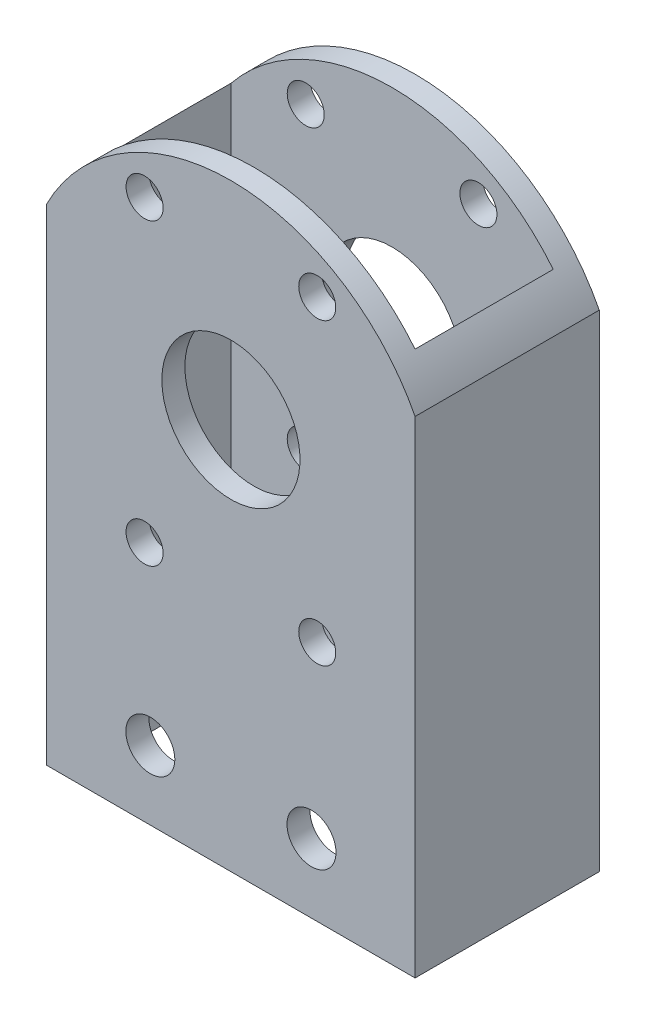
SolidWorks part; units mm, degrees
material "6061-T6 (SS)"
ref_plane "Front" through (0, 0, 0) normal (0, 0, 1) x (1, 0, 0)
ref_plane "Top" through (0, 0, 0) normal (0, 1, 0) x (1, 0, 0)
ref_plane "Right" through (0, 0, 0) normal (1, 0, 0) x (0, 0, -1)
sketch "Sketch1" plane through (0, 0, 0) normal (0, 1, 0) x (1, 0, 0)
  line L1 (-25.4, -12.7) -> (25.4, -12.7)
  line L2 (-25.4, -12.7) -> (-25.4, 12.7)
  line L3 (-25.4, 12.7) -> (25.4, 12.7)
  line L4 (25.4, -12.7) -> (25.4, 12.7)
  line L5 (-25.4, -12.7) -> (25.4, 12.7) construction
  line L6 (-25.4, 12.7) -> (25.4, -12.7) construction
  point P0 (0, 0)
  dimension "D1" = 25.4
  dimension "D2" = 50.8
extrude "Extrude-Thin1" add sketch "Sketch1" along normal blind 82.55 thin thin type one direction reverse wall 3.175
sketch "Sketch2" plane through (0, 0, -12.7) normal (0, 0, -1) x (-1, 0, 0)
  line L0 (0, 82.55) -> (0, 50.8)
  line L1 (-25.4, 82.55) -> (25.4, 82.55) construction
  line L3 (0, 41.275) -> (0, 60.325) construction
  circle A1 centre (0, 50.8) radius 23.8125
  circle A3 centre (0, 50.8) radius 9.525
  point P12 (0, 50.8)
  dimension "D1" = 19.05
  dimension "D3" = 47.625
  dimension "D2" = 31.75
hole_wizard "#10 Clearance Hole1" positions "Sketch5" profile "Sketch6" hole size "#10" standard "ANSI Inch" end condition through all
sketch "Sketch5" plane through (0, 0, -12.7) normal (0, 0, -1) x (-1, 0, 0)
  line L0 (0, 82.55) -> (0, 53.975)
  line L1 (-25.4, 82.55) -> (25.4, 82.55) construction
  line L3 (-11.9063, 74.5972) -> (11.9063, 74.5972)
  line L4 (-11.9063, 74.5972) -> (-11.9063, 33.3528)
  line L5 (-11.9063, 33.3528) -> (11.9063, 33.3528)
  line L6 (11.9063, 74.5972) -> (11.9063, 33.3528)
  circle A0 centre (0, 53.975) radius 23.8125
  point P21 (-11.9063, 74.5972)
  point P22 (11.9063, 74.5972)
  point P24 (11.9063, 33.3528)
  point P25 (-11.9063, 33.3528)
  dimension "D1" = 47.625
  dimension "D2" = 28.575
  dimension "D3" = 23.8125
sketch "Sketch6" plane through (11.9063, 33.3528, -12.7) normal (1, 0, 0) x (0, 1, 0)
  line L0 (0, 0) -> (0, 25.4)
  line L1 (0, 25.4) -> (2.5527, 25.4)
  line L2 (2.5527, 25.4) -> (2.5527, 0)
  line L5 (2.5527, 0) -> (0, 0)
  line L11 (0, -6.35) -> (0, 107.95) construction
  dimension "Thru Hole Dia." = 5.1054
  dimension "Thru Hole Depth" = 25.4
sketch "Sketch7" plane through (0, 0, -12.7) normal (0, 0, -1) x (-1, 0, 0)
  line L0 (-11.9063, 74.5972) -> (11.9063, 33.3528) construction
  circle A1 centre (0, 53.975) radius 9.525
  point P9 (0, 53.975)
  dimension "D1" = 19.05
extrude "Cut-Extrude2" cut sketch "Sketch7" against normal through all both
hole_wizard "1/4 Clearance Hole2" positions "Sketch8" profile "Sketch9" hole size "1/4" standard "ANSI Inch" end condition through all
sketch "Sketch8" plane through (0, 0, 12.7) normal (0, 0, 1) x (1, 0, 0)
  line L2 (-25.4, 82.55) -> (-25.4, 0) construction
  line L4 (-25.4, 0) -> (25.4, 0) construction
  point P0 (-11.1125, 9.525)
  point P2 (11.1125, 9.525)
  point P14 (-109.1715, 68.7854)
  dimension "D1" = 22.225
  dimension "D2" = 14.2875
  dimension "D3" = 9.525
sketch "Sketch9" plane through (-11.1125, 9.525, 12.7) normal (1, 0, 0) x (0, -1, 0)
  line L0 (0, 0) -> (0, 25.4)
  line L1 (0, 25.4) -> (3.3782, 25.4)
  line L2 (3.3782, 25.4) -> (3.3782, 0)
  line L5 (3.3782, 0) -> (0, 0)
  line L11 (0, -6.35) -> (0, 107.95) construction
  dimension "Thru Hole Dia." = 6.7564
  dimension "Thru Hole Depth" = 25.4
sketch "Sketch10" plane through (0, 0, -12.7) normal (0, 0, -1) x (-1, 0, 0)
  line L0 (-25.4, 67.0659) -> (-25.4, 82.55)
  line L1 (-25.4, 82.55) -> (25.4, 82.55)
  line L2 (25.4, 82.55) -> (25.4, 67.0659)
  line L3 (25.4, 82.55) -> (25.4, 0) construction
  arc A0 (25.4, 67.0659) -> (-25.4, 67.0659) centre (0, 53.975) ccw
  line M13 (25.4, 0) -> (25.4, 82.55)
  line M14 (25.4, 82.55) -> (-25.4, 82.55)
  line M15 (-25.4, 82.55) -> (-25.4, 0)
extrude "Cut-Extrude3" cut sketch "Sketch10" against normal through all contours A0 L1 M15 | A0 M13 M14
